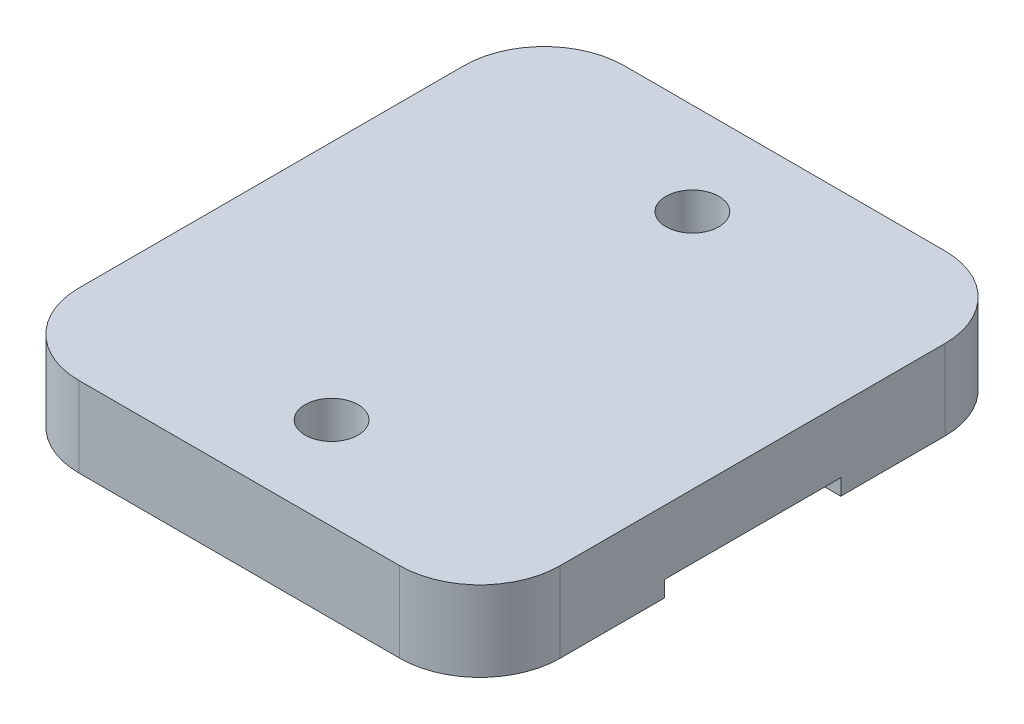
SolidWorks part; units mm, degrees
material "PLA"
ref_plane "Front Plane" through (0, 0, 0) normal (0, 0, 1) x (1, 0, 0)
ref_plane "Top Plane" through (0, 0, 0) normal (0, 1, 0) x (1, 0, 0)
ref_plane "Right Plane" through (0, 0, 0) normal (1, 0, 0) x (0, 0, -1)
ref_plane "Plane1" through (0, -5, 0) normal (0, -1, 0) x (1, 0, 0)
sketch "Sketch1" plane through (0, -5, 0) normal (0, -1, 0) x (1, 0, 0)
  line L0 (-15, 17) -> (-15, -17)
  line L1 (-15, -17) -> (15, -17)
  line L2 (15, -17) -> (15, 17)
  line L3 (15, 17) -> (-15, 17)
  line L4 (-15, 17) -> (15, -17) construction
  dimension "D1" = 30
  dimension "D2" = 34
extrude "Boss-Extrude1" add sketch "Sketch1" against normal blind 5
sketch "Sketch2" plane through (-15, 0, 0) normal (-1, 0, 0) x (0, 0, 1)
  line L0 (-5.5, -5) -> (5.5, -5)
  line L1 (5.5, -5) -> (5.5, -4)
  line L2 (5.5, -4) -> (-5.5, -4)
  line L3 (-5.5, -4) -> (-5.5, -5)
  line L5 (-17, -5) -> (17, -5) construction
  dimension "D1" = 11
  dimension "D2" = 1
extrude "Cut-Extrude1" cut sketch "Sketch2" against normal through all
fillet "Fillet1" radius 5 4 edges at (-15, -2.5, 17) (15, -2.5, 17) (-15, -2.5, -17) (15, -2.5, -17)
sketch "Sketch6" plane through (0, -5, 0) normal (0, -1, 0) x (1, 0, 0)
  line L0 (-15, 0) -> (15, 0) construction
  line L1 (-15, 5.5) -> (-15, -5.5) construction
  line L2 (15, 5.5) -> (15, -5.5) construction
  line L3 (10, 17) -> (-10, 17) construction
  line L6 (0, 17) -> (0, -17) construction
  line L7 (-10, -17) -> (10, -17) construction
  circle A4 centre (0, 11.25) radius 1.65
  circle A5 centre (0, -11.25) radius 1.65
  dimension "D6" = 5.75
extrude "Cut-Extrude2" cut sketch "Sketch6" against normal through all
